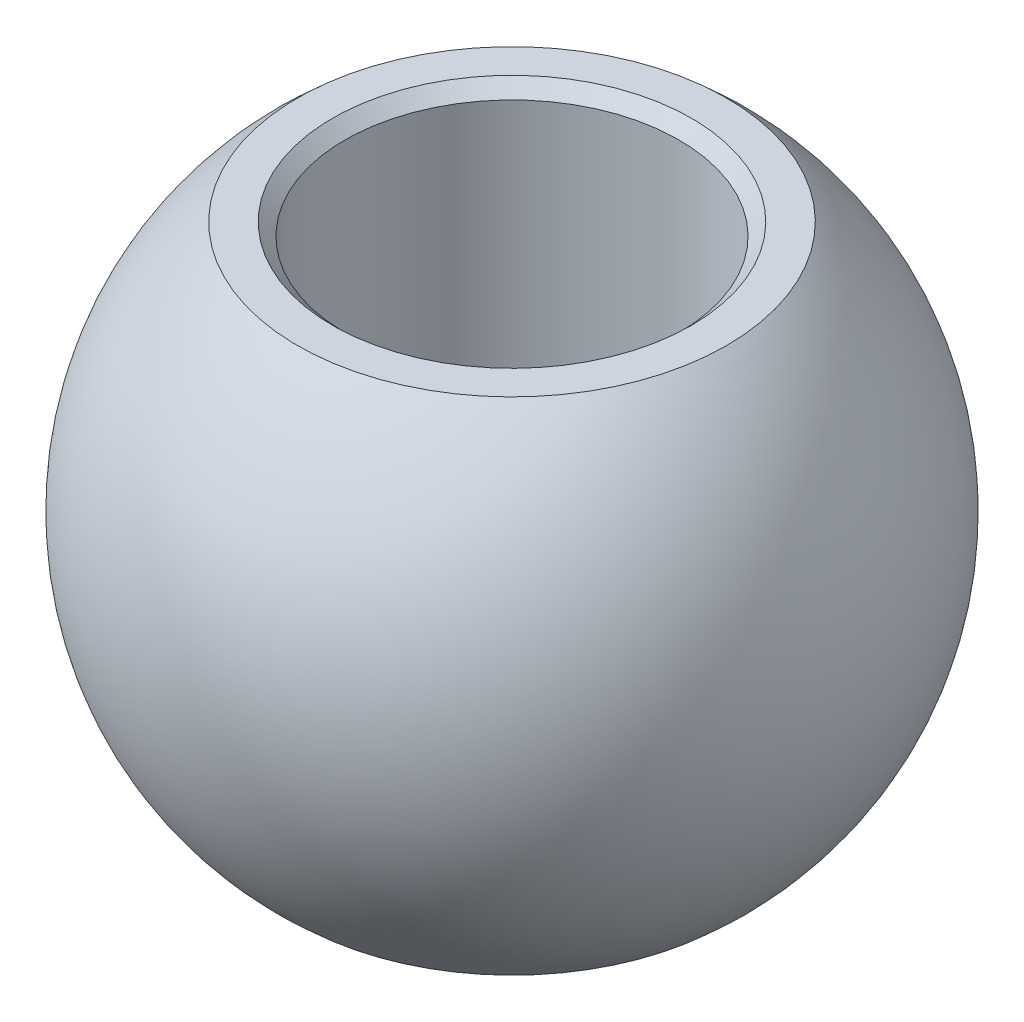
SolidWorks part; units mm, degrees
ref_plane "Front Plane" through (0, 0, 0) normal (0, 0, 1) x (1, 0, 0)
ref_plane "Top Plane" through (0, 0, 0) normal (0, 1, 0) x (1, 0, 0)
ref_plane "Right Plane" through (0, 0, 0) normal (1, 0, 0) x (0, 0, -1)
sketch "Sketch1" plane through (0, 0, 0) normal (0, 0, 1) x (1, 0, 0)
  line L0 (0, -6) -> (0, 6) construction
  line L1 (0, 0) -> (-7.9, 0) construction
  line L2 (0, 6) -> (-5.1391, 6)
  line L3 (0, -6) -> (-5.1391, -6)
  line L4 (-4, -6) -> (-4, 6)
  arc A0 (-5.1391, -6) -> (-5.1391, 6) centre (0, 0) cw
  point P4 (0, 0)
  point P12 (-4, 0)
  dimension "D1" = 7.9
  dimension "D2" = 12
  dimension "D3" = 4
revolve "Revolve1" add sketch "Sketch1" angle 360 about L0
chamfer "Chamfer1" distance 0.3 angle 45 2 edges at (4, -6, 0) (4, 6, 0)
